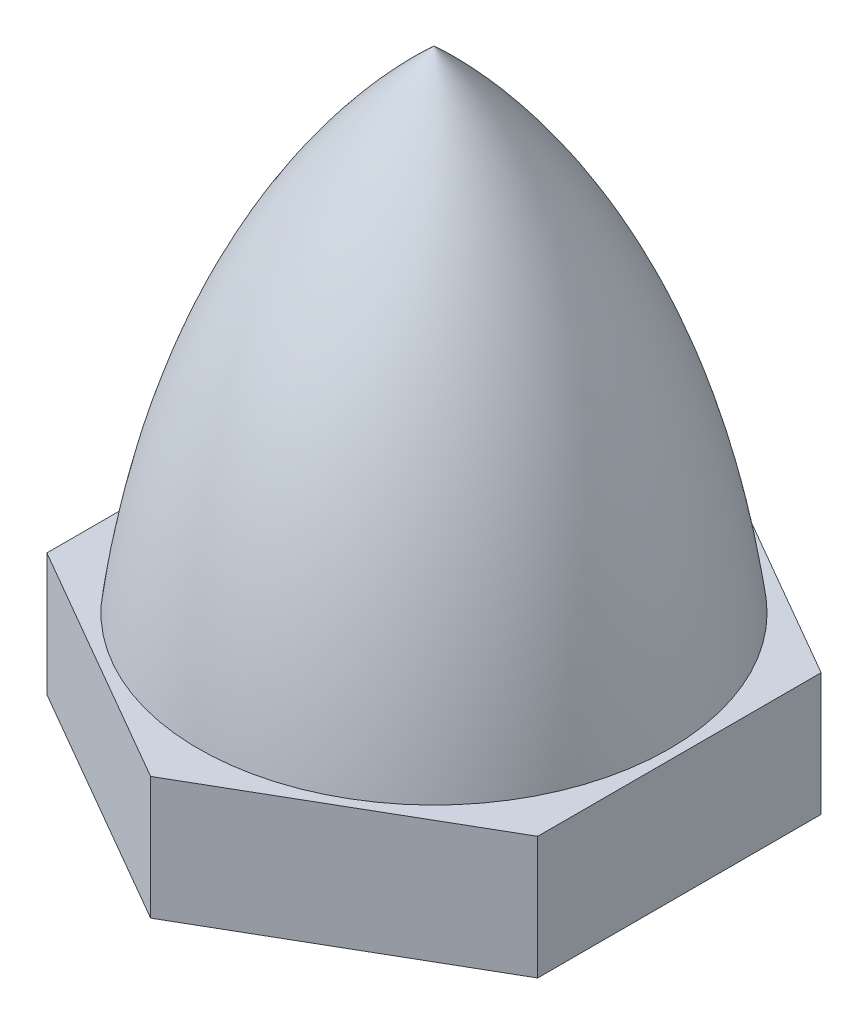
SolidWorks part; units mm, degrees
ref_plane "Спереди" through (0, 0, 0) normal (0, 0, 1) x (1, 0, 0)
ref_plane "Сверху" through (0, 0, 0) normal (0, 1, 0) x (1, 0, 0)
ref_plane "Справа" through (0, 0, 0) normal (1, 0, 0) x (0, 0, -1)
sketch "Эскиз1" plane through (0, 0, 0) normal (0, 0, 1) x (1, 0, 0)
  line L0 (0, 0) -> (0, 15)
  line L1 (0, 0) -> (6, 0)
  spline S0 degree 2 poles (0, 15) (5.663, 9.7948) (6, 0) knots 0 0 0 1 1 1
  dimension "D1" = 6
  dimension "D2" = 15
revolve "Повернуть1" add sketch "Эскиз1" angle 360 about L0
sketch "Эскиз2" plane through (0, 0, 0) normal (0, -1, 0) x (1, 0, 0)
  line L1 (0, 6.9282) -> (-6, 3.4641)
  line L2 (-6, 3.4641) -> (-6, -3.4641)
  line L3 (-6, -3.4641) -> (0, -6.9282)
  line L4 (0, -6.9282) -> (6, -3.4641)
  line L5 (6, -3.4641) -> (6, 3.4641)
  line L6 (6, 3.4641) -> (0, 6.9282)
  circle A0 centre (0, 0) radius 6 construction
  dimension "D1" = 12
extrude "Бобышка-Вытянуть1" add sketch "Эскиз2" against normal blind 3
hole_wizard "Отверстие обработанное метчиком M6x1.01" positions "Эскиз4" profile "Эскиз3" tap size "M6x1.0" standard "Ansi Metric"
sketch "Эскиз4" plane through (0, 0, 0) normal (0, -1, 0) x (-1, 0, 0)
  point P0 (0, 0)
sketch "Эскиз3" plane through (0, 0, 0) normal (1, 0, 0) x (0, 0, -1)
  line L0 (0, 0) -> (0, 9)
  line L1 (0, 9) -> (2.5, 9)
  line L2 (2.5, 9) -> (2.5, 0)
  line L5 (2.5, 0) -> (0, 0)
  line L10 (0, 9) -> (-2.5, 9) construction
  line L11 (0, -6.35) -> (0, 107.95) construction
  dimension "Диаметр сверла" = 5
  dimension "Глубина сверла" = 9
  dimension "Угол заточки сверла" = 180
cosmetic thread "Отверстие резьбы1" parameters "D1"=9, "D2"=6
